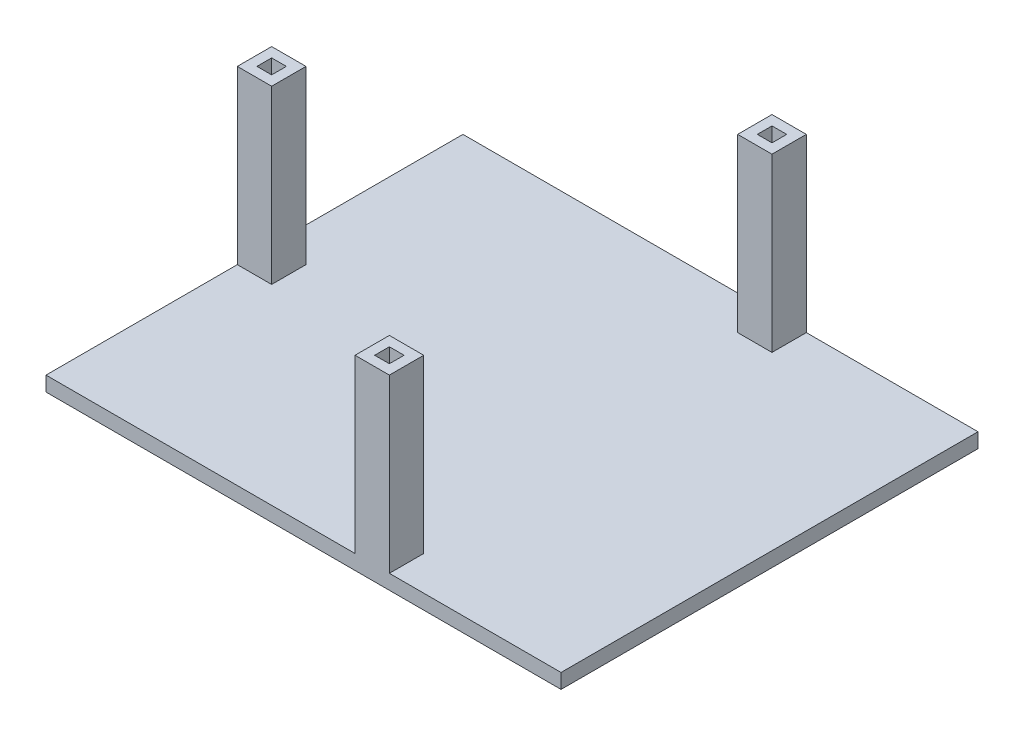
SolidWorks part; units mm, degrees
ref_plane "Front Plane" through (0, 0, 0) normal (0, 0, 1) x (1, 0, 0)
ref_plane "Top Plane" through (0, 0, 0) normal (0, 1, 0) x (1, 0, 0)
ref_plane "Right Plane" through (0, 0, 0) normal (1, 0, 0) x (0, 0, -1)
sketch "Sketch2" plane through (0, 0, 0) normal (0, 1, 0) x (1, 0, 0)
  line L0 (-54.8169, 19.6012) -> (50.1831, 19.6012)
  line L1 (50.1831, 19.6012) -> (50.1831, -65.3988)
  line L2 (-54.8169, 19.6012) -> (-54.8169, -65.3988)
  line L3 (-54.8169, -65.3988) -> (50.1831, -65.3988)
sketch "Sketch3" plane through (0, 0, 0) normal (0, 1, 0) x (1, 0, 0)
  line L0 (-54.8169, 19.6012) -> (50.1831, 19.6012)
  line L1 (50.1831, 19.6012) -> (50.1831, -65.3988)
  line L2 (50.1831, -65.3988) -> (-54.8169, -65.3988)
  line L3 (-54.8169, -65.3988) -> (-54.8169, 19.6012)
extrude "Boss-Extrude3" add sketch "Sketch3" along normal blind 3 contours L3 L0 L1 L2
ref_plane "Plane3" through (-54.8169, 3, 65.3988) normal (-1, 0, 0) x (0, 0, 1)
sketch "Sketch5" plane through (0, 3, 0) normal (0, 1, 0) x (1, 0, 0)
  line L0 (50.1831, -65.3988) -> (15.1831, -65.3988)
  line L2 (50.1831, -65.3988) -> (-54.8169, -65.3988) construction
  line L3 (15.1831, -65.3988) -> (15.1831, -58.3988)
  line L4 (15.1831, -58.3988) -> (8.1831, -58.3988)
  line L5 (8.1831, -58.3988) -> (8.1831, -65.3988)
  line L6 (10.1831, -60.3988) -> (10.1831, -63.3988)
  line L14 (13.1831, -60.3988) -> (13.1831, -63.3988)
  line L15 (13.1831, -60.3988) -> (10.1831, -60.3988)
  line L16 (10.1831, -63.3988) -> (13.1831, -63.3988)
  line L17 (8.1831, -65.3988) -> (15.1831, -65.3988)
  line M10 (-54.8169, -65.3988) -> (50.1831, -65.3988)
extrude "Boss-Extrude4" add sketch "Sketch5" along normal blind 35 contours L4 L5 L3 L16 L6 L15 L14 M10
sketch "Sketch9" plane through (0, 3, 0) normal (0, 1, 0) x (1, 0, 0)
  line L0 (50.1831, 19.6012) -> (15.1831, 19.6012)
  line L1 (-54.8169, 19.6012) -> (50.1831, 19.6012) construction
  line L2 (15.1831, 19.6012) -> (15.1831, 12.6012)
  line L3 (15.1831, 12.6012) -> (8.1831, 12.6012)
  line L4 (8.1831, 12.6012) -> (8.1831, 19.6012)
  line L5 (8.1831, 19.6012) -> (15.1831, 19.6012)
  line L6 (15.1831, 19.6012) -> (8.1831, 19.6012)
  line L7 (8.1831, 19.6012) -> (15.1831, 19.6012)
  line L8 (8.1831, 19.6012) -> (8.1831, 17.6003)
  line L9 (13.1873, 17.6003) -> (10.1884, 17.6003)
  line L11 (13.1873, 17.6003) -> (13.1873, 14.605)
  line L12 (13.1873, 14.605) -> (10.1884, 14.605)
  line L13 (10.1884, 14.605) -> (10.1884, 17.6003)
  line M7 (50.1831, 19.6012) -> (-54.8169, 19.6012)
extrude "Boss-Extrude5" add sketch "Sketch9" along normal blind 35 contours L4 L3 L2 L12 L13 L9 L11 M7
sketch "Sketch11" plane through (0, 3, 0) normal (0, 1, 0) x (1, 0, 0)
  line L0 (-54.8169, -65.3988) -> (-54.8169, 19.6012) construction
  line L1 (-54.8169, 19.6012) -> (-54.8169, -19.3988)
  line L2 (-54.8169, -19.3988) -> (-47.8169, -19.3988)
  line L3 (-47.8169, -19.3988) -> (-47.8169, -26.3988)
  line L4 (-47.8169, -26.3988) -> (-54.8169, -26.3988)
  line L5 (-54.8169, -26.3988) -> (-54.8169, -19.3988)
  line L8 (-49.8169, -21.3988) -> (-49.8169, -24.3988)
  line L9 (-49.8169, -24.3988) -> (-52.8169, -24.3988)
  line L10 (-52.8169, -24.3988) -> (-52.8169, -21.3988)
  line L11 (-52.8169, -21.3988) -> (-49.8169, -21.3988)
  line M15 (-54.8169, 19.6012) -> (-54.8169, -65.3988)
extrude "Boss-Extrude6" add sketch "Sketch11" along normal blind 35 contours L4 L3 L2 L10 L11 L8 L9 M15
